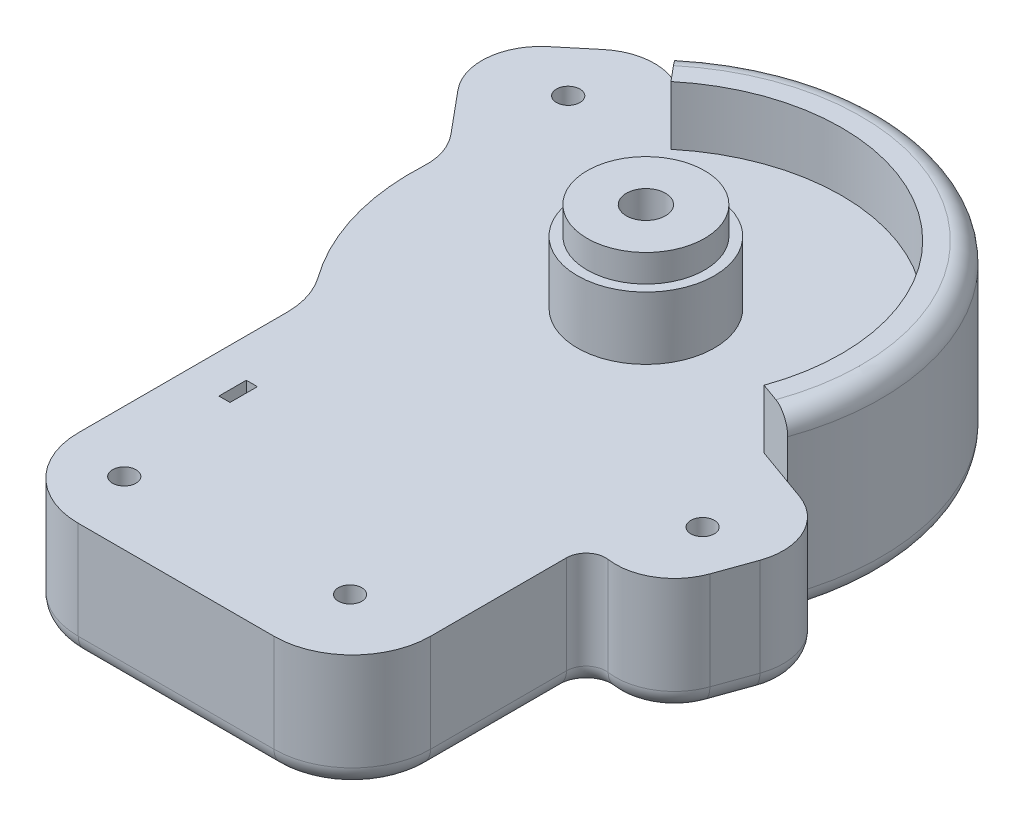
SolidWorks part; units mm, degrees
ref_plane "Front Plane" through (0, 0, 0) normal (0, 0, 1) x (1, 0, 0)
ref_plane "Top Plane" through (0, 0, 0) normal (0, 1, 0) x (1, 0, 0)
ref_plane "Right Plane" through (0, 0, 0) normal (1, 0, 0) x (0, 0, -1)
sketch "Sketch1" plane through (0, 0, 0) normal (0, -1, 0) x (-1, 0, 0)
  line L8 (-155.9788, -669.5716) -> (-160.6854, -671.2593)
  line L9 (-166.367, -699.855) -> (-169.7423, -690.4419)
  line L10 (-144.4999, -714.6026) -> (-144.4999, -749.3201)
  line L11 (-124.4999, -769.3201) -> (-74.4999, -769.3201)
  line L12 (-54.4999, -695.957) -> (-54.4999, -749.3201)
  line L13 (-57.8879, -599.3857) -> (-61.0888, -603.2268)
  line L14 (-36.7618, -597.4652) -> (-29.0796, -603.867)
  line L15 (-36.1279, -635.7557) -> (-27.159, -624.9931)
  arc A10 (-36.1279, -635.7557) -> (-39.5836, -646.1508) centre (-24.6046, -645.3585) ccw
  arc A11 (-160.6854, -671.2593) -> (-169.7423, -690.4419) centre (-155.6225, -685.379) ccw
  arc A12 (-166.367, -699.855) -> (-150.1867, -709.65) centre (-152.2473, -694.7922) ccw
  arc A13 (-144.4999, -714.6026) -> (-150.1867, -709.65) centre (-149.4999, -714.6026) ccw
  arc A14 (-144.4999, -749.3201) -> (-124.4999, -769.3201) centre (-124.4999, -749.3201) ccw
  arc A15 (-74.4999, -769.3201) -> (-54.4999, -749.3201) centre (-74.4999, -749.3201) ccw
  arc A16 (-50.7499, -684.2978) -> (-54.4999, -695.957) centre (-34.4999, -695.957) ccw
  arc A17 (-50.7499, -684.2978) -> (-39.5836, -646.1508) centre (-99.4999, -649.3201) ccw
  arc A18 (-36.7618, -597.4652) -> (-57.8879, -599.3857) centre (-46.3646, -608.9885) ccw
  arc A19 (-27.159, -624.9931) -> (-29.0796, -603.867) centre (-38.6823, -615.3903) ccw
  arc A20 (-155.9788, -669.5716) -> (-61.0888, -603.2268) centre (-99.4999, -649.3201) cw
extrude "Boss-Extrude1" add sketch "Sketch1" along normal blind 30
sketch "Sketch3" plane through (0, -30, 0) normal (0, -1, 0) x (1, 0, 0)
  circle A0 centre (42.5234, 612.1894) radius 6
  circle A1 centre (155.0926, 690.4309) radius 6
  circle A2 centre (124.9764, 750.3578) radius 6
  circle A3 centre (70.026, 753.0951) radius 6
extrude "Cut-Extrude2" cut sketch "Sketch3" against normal blind 10
sketch "Sketch4" plane through (0, -20, 0) normal (0, -1, 0) x (1, 0, 0)
  circle A0 centre (42.5234, 612.1894) radius 3
  circle A1 centre (155.0926, 690.4309) radius 3
  circle A2 centre (124.9764, 750.3578) radius 3
  circle A3 centre (70.026, 753.0951) radius 3
extrude "Cut-Extrude3" cut sketch "Sketch4" against normal up to next
sketch "Sketch5" plane through (0, 0, 0) normal (0, 1, 0) x (1, 0, 0)
  circle A0 centre (99.4999, -649.3201) radius 17.5
extrude "Boss-Extrude2" add sketch "Sketch5" along normal blind 16
sketch "Sketch6" plane through (0, 16, 0) normal (0, 1, 0) x (1, 0, 0)
  circle A0 centre (99.4999, -649.3201) radius 15
extrude "Boss-Extrude3" add sketch "Sketch6" along normal blind 7
sketch "Sketch7" plane through (0, 0, 0) normal (0, 1, 0) x (1, 0, 0)
  line L0 (155.9788, -669.5716) -> (146.5656, -666.1964)
  line L1 (67.4906, -610.909) -> (61.0888, -603.2268)
  arc A0 (155.9788, -669.5716) -> (61.0888, -603.2268) centre (99.4999, -649.3201) ccw
  arc A1 (146.5656, -666.1964) -> (67.4906, -610.909) centre (99.4998, -649.3201) ccw
extrude "Boss-Extrude4" add sketch "Sketch7" along normal blind 15
fillet "Fillet1" radius 5 20 edges at (158.3321, -30, 670.4154) (169.1867, -30, 678.9748) (168.0547, -30, 695.1485) (160.0152, -30, 707.6241) (146.2161, -30, 710.832) (144.4999, -30, 731.9613) (138.642, -30, 763.4622) (99.4999, -30, 769.3201) (60.3577, -30, 763.4622) (59.4883, -30, 601.3063) (47.7226, -30, 594.0501) (32.9207, -30, 600.6661) (23.7439, -30, 614.0323) (31.6435, -30, 630.3744) (38.8386, -30, 640.6265) (41.9161, -30, 666.1758) (53.5393, -30, 689.8333) (133.8804, -30, 600.1471) (54.4999, -30, 722.6385) (133.8804, 15, 600.1471)
sketch "Sketch8" plane through (0, 23, 0) normal (0, 1, 0) x (1, 0, 0)
  circle A0 centre (99.4999, -649.3201) radius 5
extrude "Cut-Extrude4" cut sketch "Sketch8" against normal up to next
sketch "Sketch9" plane through (0, 0, 0) normal (0, 1, 0) x (1, 0, 0)
  line L1 (64.3305, -716.2201) -> (67.1685, -716.2201)
  line L2 (64.3305, -716.2201) -> (64.3305, -723.2201)
  line L3 (64.3305, -723.2201) -> (67.1685, -723.2201)
  line L4 (67.1685, -716.2201) -> (67.1685, -723.2201)
extrude "Cut-Extrude5" cut sketch "Sketch9" against normal up to next
sketch "Sketch11" plane through (0, -30, 0) normal (0, -1, 0) x (1, 0, 0)
  line L0 (67.1685, 716.2201) -> (87.1685, 716.2201)
  line L1 (67.1685, 716.2201) -> (67.1685, 723.2201)
  line L2 (67.1685, 723.2201) -> (87.1685, 723.2201)
  line L3 (103.4499, 649.3201) -> (95.5499, 649.3201)
  line L4 (95.5499, 649.3201) -> (95.5499, 709.3201)
  line L5 (103.4499, 649.3201) -> (103.4499, 709.3201)
  arc A0 (87.1685, 716.2201) -> (95.5499, 709.3201) centre (87.9092, 708.5794) cw
  arc A1 (87.1685, 723.2201) -> (103.4499, 709.3201) centre (88.3592, 708.1294) cw
  point P10 (99.4999, 649.3201)
extrude "Cut-Extrude6" cut sketch "Sketch11" against normal blind 10
